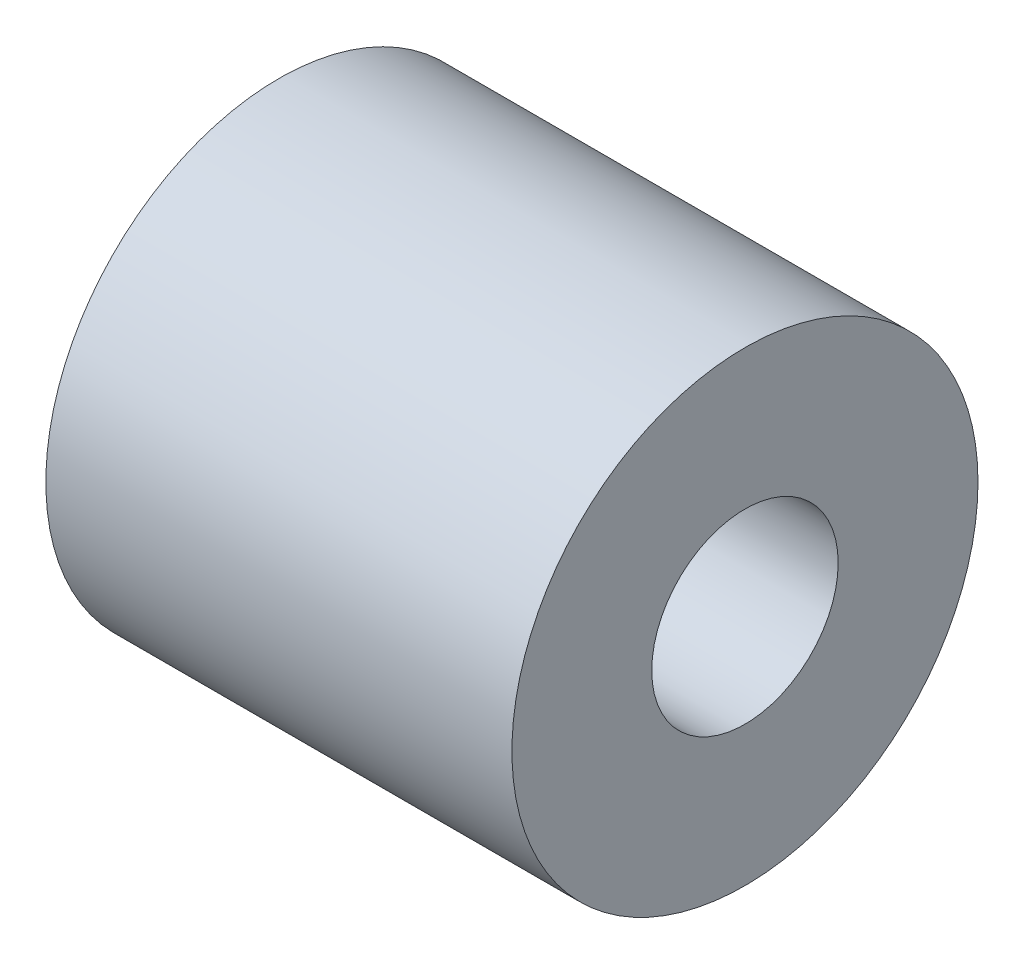
SolidWorks part; units mm, degrees
ref_plane "Front" through (0, 0, 0) normal (0, 0, 1) x (1, 0, 0)
ref_plane "Top" through (0, 0, 0) normal (0, 1, 0) x (1, 0, 0)
ref_plane "Right" through (0, 0, 0) normal (1, 0, 0) x (0, 0, -1)
sketch "Sketch1" plane through (0, 0, 0) normal (1, 0, 0) x (0, 0, -1)
  circle A0 centre (0, 0) radius 1
  circle A1 centre (0, 0) radius 2.5
  dimension "D1" = 2
  dimension "D2" = 5
extrude "Boss-Extrude1" add sketch "Sketch1" along normal blind 5
